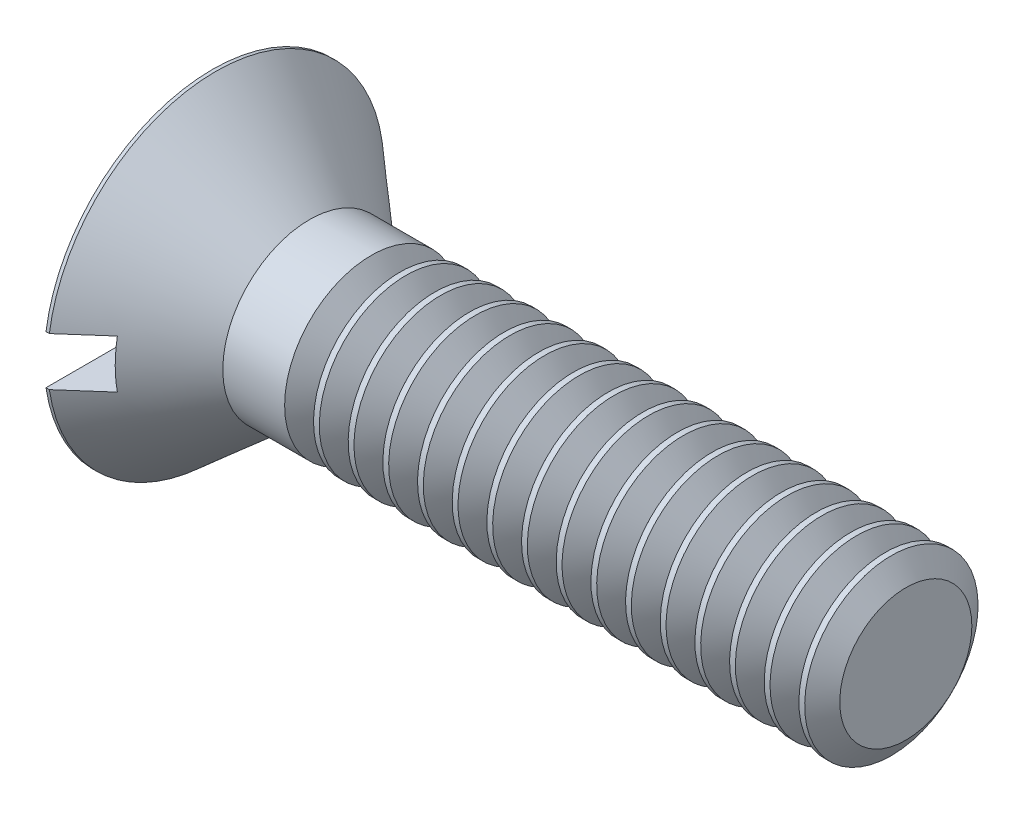
SolidWorks part; units mm, degrees
revolve "Base-Revolve" add sketch "BodySke" angle 360 about L5
sketch "BodySke" plane through (0, 0, 0) normal (0, 0, 1) x (1, 0, 0)
  line L0 (0, 0) -> (0, 6.1595)
  line L1 (0, 6.1595) -> (0.1227, 6.1595)
  line L2 (3.556, 3.175) -> (25.4, 3.175)
  line L3 (25.4, 3.175) -> (25.4, 0)
  line L4 (25.4, 0) -> (0, 0)
  line L5 (-6.35, 0) -> (82.55, 0) construction
  line L6 (3.556, -3.175) -> (25.4, -3.175) construction
  line L7 (0.1227, -6.1595) -> (3.556, -3.175) construction
  line L8 (0.1227, 6.1595) -> (3.556, 3.175)
  line L9 (0, -6.1595) -> (0.1227, -6.1595) construction
  line L10 (4.826, 4.7625) -> (4.826, -4.7625) construction
  line L11 (6.35, 6.35) -> (6.35, -3.175) construction
  dimension "Diameter" = 6.35
  dimension "Length" = 25.4
  dimension "Head_ht" = 3.556
  dimension "Head_dia" = 12.319
  dimension "Head_ang" = 82
  dimension "D6" = 0.1227
  dimension "Advance" = 1.27
  dimension "Thread_nom" = 19.05
cosmetic thread "ThreadCosmetic" [suppressed] parameters "Thread_length"=19.05, "Thread_minor"=4.8387
extrude "Slot" cut sketch "Sketch6" against normal blind 1.4478
sketch "Sketch6" plane through (0, 0, 0) normal (-1, 0, 0) x (0, 0, 1)
  line L0 (-6.1595, -0.889) -> (6.1595, -0.889)
  line L1 (-6.1595, -0.889) -> (-6.1595, 0.889)
  line L2 (6.1595, 0.889) -> (-6.1595, 0.889)
  line L3 (6.1595, 0.889) -> (6.1595, -0.889)
  dimension "Slot_width" = 1.778
  dimension "D1" = 0.889
  dimension "D2" = 12.319
  dimension "D3" = 6.1595
ref_plane "Plane1" through (0, 0, 0) normal (0, 0, 1) x (1, 0, 0)
ref_plane "Plane2" through (0, 0, 0) normal (0, 1, 0) x (1, 0, 0)
ref_plane "Plane3" through (0, 0, 0) normal (1, 0, 0) x (0, 0, -1)
other "Configuration Table"
sketch "ThdSchSke" plane through (0, 0, 0) normal (0, 0, 1) x (1, 0, 0)
  line L0 (6.35, -2.4194) -> (5.8209, -3.175)
  line L1 (6.35, -2.4194) -> (6.8791, -3.175)
  line L2 (6.8791, -3.175) -> (6.8791, -3.9688)
  line L3 (-3.175, 0) -> (5.1513, 0) construction
  line L5 (6.8791, -3.9688) -> (5.8209, -3.9688)
  line L6 (5.8209, -3.9688) -> (5.8209, -3.175)
  line L7 (0, 6.1595) -> (0, 0.889) construction
  dimension "Diameter" = 6.35
  dimension "Thread_minor" = 4.8387
  dimension "Start" = 6.35
revolve "ThreadSchematic" cut sketch "ThdSchSke" angle 360 about L3
pattern_linear "ThdSchPat" count 16 spacing 1.27 along (1, 0, 0) of "ThreadSchematic"
equation "\"D1@Sketch6\" = \"Slot_width@Sketch6\" / 2"
equation "\"D2@Sketch6\" = \"Head_dia@BodySke\""
equation "\"D3@Sketch6\" = \"D2@Sketch6\" / 2"
equation "\"Thread_length@ThreadCosmetic\" = ((sgn( (\"Length@BodySke\" - \"Advance@BodySke\" - \"Head_ht@BodySke\" ) - \"Thread_nom@BodySke\" )-1)*( (\"Length@BodySke\" - \"Advance@BodySke\" - \"Head_ht@BodySke\" ) - \"Thread_nom@BodySke\" ))/-2+ \"Thread_nom@BodySke\""
equation "\"Thread_minor@ThdSchSke\" = \"Thread_minor@ThreadCosmetic\""
equation "\"Diameter@ThdSchSke\" = \"Diameter@BodySke\""
equation "\"Overcut@ThdSchSke\" = \"Diameter@BodySke\" * 1.25"
equation "\"Start@ThdSchSke\" = 0.000001 + \"Length@BodySke\" - \"Thread_length@ThreadCosmetic\"  '---Countersunk---"
equation "\"Num_threads@ThdSchPat\" = int( \"Thread_length@ThreadCosmetic\" / \"Advance@BodySke\" + 0.999 )  + 1"
equation "\"Advance@ThdSchPat\" = \"Thread_length@ThreadCosmetic\" /  (\"Num_threads@ThdSchPat\" - 1) 'relax it"
